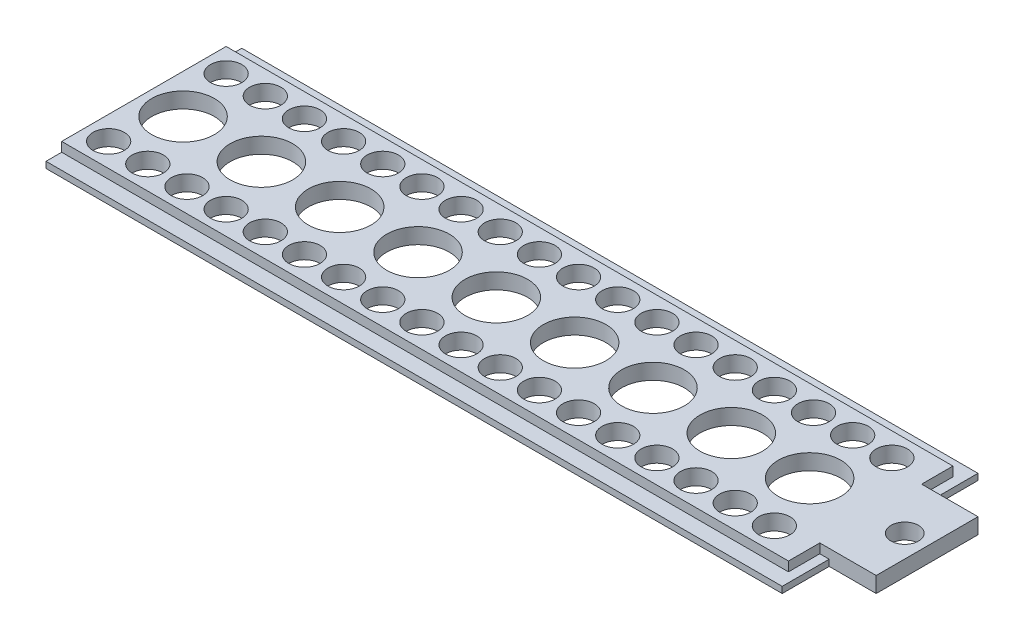
SolidWorks part; units mm, degrees
ref_plane "Ebene vorne" through (0, 0, 0) normal (0, 0, 1) x (1, 0, 0)
ref_plane "Ebene oben" through (0, 0, 0) normal (0, 1, 0) x (1, 0, 0)
ref_plane "Ebene rechts" through (0, 0, 0) normal (1, 0, 0) x (0, 0, -1)
sketch "Skizze1" plane through (0, 0, 0) normal (1, 0, 0) x (0, 0, -1)
  line L1 (-40.6559, -25.3697) -> (-15.6559, -25.3697)
  line L2 (-40.6559, -25.3697) -> (-40.6559, -27.3697)
  line L3 (-40.6559, -27.3697) -> (-15.6559, -27.3697)
  line L4 (-15.6559, -25.3697) -> (-15.6559, -27.3697)
  dimension "D1" = 2
  dimension "D2" = 25
extrude "Aufsatz-Linear austragen1" add sketch "Skizze1" along normal blind 100
sketch "Skizze2" plane through (0, 0, 0) normal (-1, 0, 0) x (0, 0, 1)
  line L1 (15.6559, -25.3697) -> (17.6559, -25.3697)
  line L2 (15.6559, -25.3697) -> (15.6559, -26.5697)
  line L3 (15.6559, -26.5697) -> (17.6559, -26.5697)
  line L4 (17.6559, -25.3697) -> (17.6559, -26.5697)
  line L5 (40.6559, -25.3697) -> (38.6559, -25.3697)
  line L6 (40.6559, -25.3697) -> (40.6559, -26.5697)
  line L7 (40.6559, -26.5697) -> (38.6559, -26.5697)
  line L8 (38.6559, -25.3697) -> (38.6559, -26.5697)
  dimension "D1" = 2
  dimension "D2" = 1.2
  dimension "D3" = 2
  dimension "D4" = 1.2
extrude "Schnitt-Linear austragen1" cut sketch "Skizze2" against normal through all
sketch "Skizze3" plane through (0, -25.3697, 0) normal (0, 1, 0) x (1, 0, 0)
  line L0 (100, -17.6559) -> (100, -38.6559) construction
  line L1 (100, -21.6559) -> (94, -21.6559)
  line L2 (100, -21.6559) -> (100, -15.6559)
  line L3 (100, -15.6559) -> (94, -15.6559)
  line L4 (94, -21.6559) -> (94, -15.6559)
  line L5 (100, -15.6559) -> (0, -15.6559) construction
  line L6 (100, -40.6559) -> (0, -40.6559) construction
  line L7 (100, -34.6559) -> (94, -34.6559)
  line L8 (100, -34.6559) -> (100, -40.6559)
  line L9 (100, -40.6559) -> (94, -40.6559)
  line L10 (94, -34.6559) -> (94, -40.6559)
  circle A0 centre (97.15, -28.1559) radius 1.75
  dimension "D6" = 3.5
  dimension "D7" = 2.85
  dimension "D1" = 12.5
  dimension "D2" = 6
  dimension "D3" = 0
  dimension "D4" = 6
  dimension "D5" = 6
extrude "Schnitt-Linear austragen2" cut sketch "Skizze3" against normal through all
sketch "Skizze4" plane through (94, 0, 0) normal (1, 0, 0) x (0, 0, -1)
  line L0 (-34.6559, -27.3697) -> (-34.6559, -25.3697) construction
  line L1 (-38.6559, -25.3697) -> (-34.6559, -25.3697)
  line L2 (-38.6559, -25.3697) -> (-38.6559, -26.5697)
  line L3 (-38.6559, -26.5697) -> (-34.6559, -26.5697)
  line L4 (-34.6559, -25.3697) -> (-34.6559, -26.5697)
  line L5 (-21.6559, -27.3697) -> (-21.6559, -25.3697) construction
  line L6 (-17.6559, -25.3697) -> (-21.6559, -25.3697)
  line L7 (-17.6559, -25.3697) -> (-17.6559, -26.5697)
  line L8 (-17.6559, -26.5697) -> (-21.6559, -26.5697)
  line L9 (-21.6559, -25.3697) -> (-21.6559, -26.5697)
  line L10 (-40.6559, -26.5697) -> (-38.6559, -26.5697) construction
  line L11 (-17.6559, -26.5697) -> (-15.6559, -26.5697) construction
  dimension "D1" = 0
  dimension "D2" = 0
extrude "Schnitt-Linear austragen3" cut sketch "Skizze4" against normal blind 1.2
sketch "Skizze5" plane through (0, -25.3697, 0) normal (0, 1, 0) x (1, 0, 0)
  line L0 (92.8, -17.6559) -> (0, -17.6559) construction
  line L1 (92.8, -38.6559) -> (0, -38.6559) construction
  line L2 (0, -17.6559) -> (0, -38.6559) construction
  circle A0 centre (3, -20.6559) radius 2
  circle A1 centre (5, -28.1559) radius 4
  circle A2 centre (3, -35.6559) radius 2
  circle A3 centre (8, -35.6559) radius 2
  circle A4 centre (8, -20.6559) radius 2
  dimension "D4" = 4
  dimension "D6" = 4
  dimension "D8" = 8
  dimension "D10" = 4
  dimension "D11" = 4
  dimension "D1" = 3
  dimension "D2" = 3
  dimension "D3" = 3
  dimension "D5" = 7.5
  dimension "D7" = 3
  dimension "D9" = 5
  dimension "D12" = 5
  dimension "D13" = 5
extrude "Schnitt-Linear austragen4" cut sketch "Skizze5" against normal through all
pattern_linear "Lineares Muster1" count 9 spacing 10 along (1, 0, 0) of "Schnitt-Linear austragen4"
